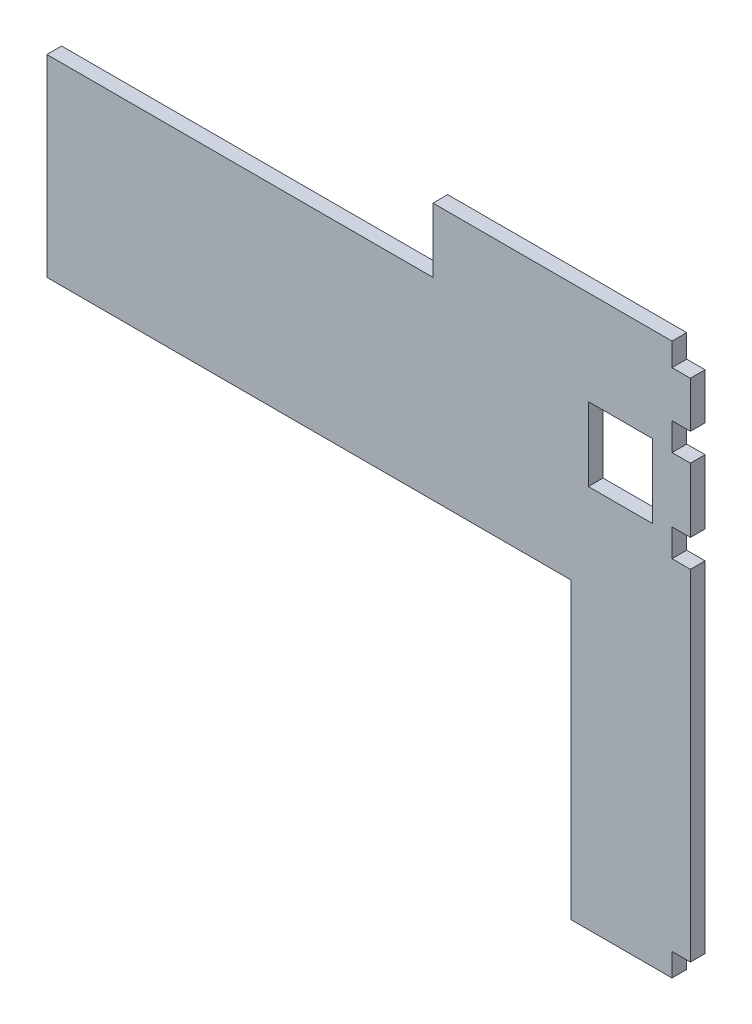
SolidWorks part; units mm, degrees
ref_plane "Front Plane" through (0, 0, 0) normal (0, 0, 1) x (1, 0, 0)
ref_plane "Top Plane" through (0, 0, 0) normal (0, 1, 0) x (1, 0, 0)
ref_plane "Right Plane" through (0, 0, 0) normal (1, 0, 0) x (0, 0, -1)
sketch "Sketch1" plane through (0, 0, 0) normal (0, 0, 1) x (1, 0, 0)
  line L1 (0, 0) -> (680, 0)
  line L2 (0, 0) -> (0, 560)
  line L3 (0, 560) -> (680, 560)
  line L4 (680, 0) -> (680, 560)
  dimension "D1" = 560
  dimension "D2" = 680
extrude "Boss-Extrude1" add sketch "Sketch1" along normal blind 16
sketch "Sketch2" plane through (0, 0, 16) normal (0, 0, 1) x (1, 0, 0)
  line L0 (680, 0) -> (680, 560) construction
  line L1 (130, 0) -> (680, 0)
  line L2 (130, 0) -> (130, -20)
  line L3 (130, -20) -> (680, -20)
  line L4 (680, 0) -> (680, -20)
  line L7 (680, 560) -> (130, 560)
  line L8 (680, 560) -> (680, 580)
  line L9 (680, 580) -> (130, 580)
  line L10 (130, 560) -> (130, 580)
  dimension "D1" = 550
  dimension "D2" = 20
extrude "Boss-Extrude2" add sketch "Sketch2" against normal blind 16
sketch "Sketch3" plane through (0, 0, 16) normal (0, 0, 1) x (1, 0, 0)
  line L0 (680, 580) -> (130, 580) construction
  line L1 (659, 397.5) -> (589, 397.5)
  line L2 (659, 397.5) -> (659, 477.5)
  line L3 (659, 477.5) -> (589, 477.5)
  line L4 (589, 397.5) -> (589, 477.5)
  line L5 (680, -20) -> (680, 580) construction
  dimension "D1" = 80
  dimension "D2" = 70
  dimension "D3" = 102.5
  dimension "D4" = 21
extrude "Cut-Extrude1" cut sketch "Sketch3" against normal through all
sketch "Sketch4" plane through (0, 0, 16) normal (0, 0, 1) x (1, 0, 0)
  line L0 (130, -20) -> (680, -20) construction
  line L1 (570, -20) -> (0, -20)
  line L3 (570, 300) -> (0, 300)
  line L4 (0, -20) -> (0, 300)
  line L5 (0, 560) -> (0, 0) construction
  line L6 (570, 300) -> (570, -20)
  line L11 (680, 580) -> (130, 580) construction
  line L12 (570, 580) -> (0, 580)
  line L13 (570, 580) -> (570, 510)
  line L14 (570, 510) -> (0, 510)
  line L15 (0, 580) -> (0, 510)
  dimension "D1" = 320
  dimension "D2" = 570
  dimension "D3" = 70
extrude "Cut-Extrude2" cut sketch "Sketch4" against normal up to next
sketch "Sketch5" plane through (0, 0, 16) normal (0, 0, 1) x (1, 0, 0)
  line L0 (680, -20) -> (680, 580) construction
  line L1 (680, 555) -> (700, 555)
  line L2 (680, 555) -> (680, 505)
  line L3 (680, 505) -> (700, 505)
  line L4 (700, 555) -> (700, 505)
  line L5 (680, 580) -> (570, 580) construction
  line L6 (570, -20) -> (680, -20) construction
  line L7 (680, 475) -> (700, 475)
  line L8 (680, 475) -> (680, 405)
  line L9 (680, 405) -> (700, 405)
  line L10 (700, 475) -> (700, 405)
  line L11 (680, 5) -> (700, 5)
  line L12 (680, 5) -> (680, 375)
  line L13 (680, 375) -> (700, 375)
  line L14 (700, 5) -> (700, 375)
  dimension "D1" = 25
  dimension "D2" = 50
  dimension "D3" = 20
  dimension "D4" = 30
  dimension "D5" = 70
  dimension "D6" = 30
  dimension "D7" = 25
extrude "Boss-Extrude3" add sketch "Sketch5" against normal up to surface (16 mm away) up to face at (455, 342.5, 0)
sketch "Sketch6" plane through (0, 0, 16) normal (0, 0, 1) x (1, 0, 0)
  line L0 (0, 510) -> (570, 510) construction
  line L1 (570, 580) -> (420, 580)
  line L2 (570, 580) -> (570, 510)
  line L3 (570, 510) -> (420, 510)
  line L4 (420, 580) -> (420, 510)
  dimension "D1" = 150
extrude "Boss-Extrude4" add sketch "Sketch6" against normal up to surface (16 mm away) up to face at (596, 369, 0)
